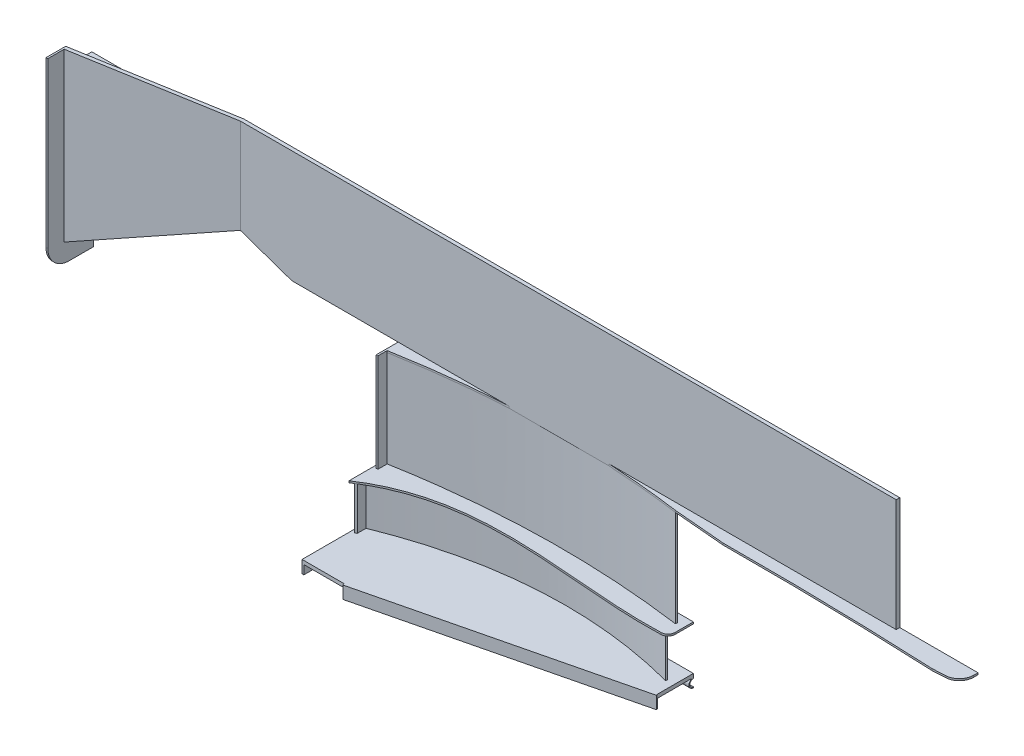
SolidWorks part; units mm, degrees
material "Elastyczna pianka poliuretanowa"
ref_plane "Płaszczyzna XY" through (0, 0, 0) normal (0, 0, 1) x (1, 0, 0)
ref_plane "Płaszczyzna XZ" through (0, 0, 0) normal (0, 1, 0) x (1, 0, 0)
ref_plane "Płaszczyzna YZ" through (0, 0, 0) normal (1, 0, 0) x (0, 0, -1)
sketch "Szkic1" plane through (0, 0, 0) normal (0, 1, 0) x (1, 0, 0)
  line L0 (212.0804, -65) -> (-1629.5, -65)
  line L1 (212.0804, -65) -> (212.0804, -55)
  line L3 (212.0804, -55) -> (-1629.5, -55)
  line L4 (-1629.5, -55) -> (-1629.5, -65)
  dimension "D1" = 10
extrude "Dodanie-wyciągnięcie1" add sketch "Szkic1" against normal blind 315
sketch "Szkic2" plane through (0, -315, 0) normal (0, -1, 0) x (1, 0, 0)
  line L0 (-1189.8241, 55) -> (82.699, 55)
  line L1 (-1189.8241, 55) -> (-1189.8241, 215)
  line L4 (212.0804, 55) -> (-1629.5, 55) construction
  line L5 (82.699, 125) -> (82.699, 55)
  spline S0 degree 2 poles (82.699, 125) (-575.049, 24.9797) (-1189.8241, 215) knots 0 0 0 1 1 1
  dimension "D1" = 160
  dimension "D2" = 70
extrude "Dodanie-wyciągnięcie2" add sketch "Szkic2" along normal blind 5
sketch "Szkic4" plane through (0, -320, 0) normal (0, -1, 0) x (1, 0, 0)
  line L2 (-1182.1774, 101.7712) -> (-1182.1774, 96.7712)
  line L3 (-385.9493, 84.8158) -> (-385.9493, 79.8158)
  spline S0 degree 2 poles (-385.9493, 84.8158) (-787.3305, 30.0926) (-1182.1774, 101.7712) knots 0 0 0 1 1 1
  spline S1 degree 2 poles (-385.9493, 79.8158) (-787.3305, 25.0926) (-1182.1774, 96.7712) knots 0 0 0 1 1 1
  dimension "D3" = 5
  dimension "D1" = 5
  dimension "D2" = 5
extrude "Dodanie-wyciągnięcie4" add sketch "Szkic4" along normal blind 270
sketch "Szkic5" plane through (0, -590, 0) normal (0, -1, 0) x (1, 0, 0)
  line L6 (-1189.8241, 195) -> (-1189.8241, 55)
  line L7 (-1189.8241, 55) -> (-365.6656, 55)
  line L8 (-365.6656, 55) -> (-365.6656, 125)
  spline S0 degree 3 poles (-1189.8241, 195) (-948.4635, 33.502) (-627.9265, 141.4858) (-365.6656, 125) knots 0 0 0 0 1 1 1 1
  dimension "D2" = 70
  dimension "D1" = 140
extrude "Dodanie-wyciągnięcie5" add sketch "Szkic5" along normal blind 5
sketch "Szkic6" plane through (0, -595, 0) normal (0, -1, 0) x (1, 0, 0)
  line L1 (-1180.7317, 163.4647) -> (-1180.7317, 158.4647)
  line L2 (-386.7114, 111.4299) -> (-386.7114, 106.4299)
  spline S0 degree 2 poles (-386.7114, 111.4299) (-791.4105, 5.1463) (-1180.7317, 163.4647) knots 0 0 0 1 1 1
  spline S1 degree 2 poles (-386.7114, 106.4299) (-791.4105, 0.1463) (-1180.7317, 158.4647) knots 0 0 0 1 1 1
  dimension "D1" = 5
  dimension "D2" = 5
  dimension "D3" = 5
extrude "Dodanie-wyciągnięcie6" add sketch "Szkic6" along normal blind 120
sketch "Szkic7" plane through (0, -715, 0) normal (0, -1, 0) x (1, 0, 0)
  line L0 (-1189.8241, 55) -> (-365.6656, 55)
  line L1 (-365.6656, 55) -> (-365.6656, 155)
  line L2 (-365.6656, 155) -> (-1189.8241, 355)
  line L3 (-1189.8241, 355) -> (-1189.8241, 55)
  dimension "D1" = 100
  dimension "D2" = 300
extrude "Dodanie-wyciągnięcie7" add sketch "Szkic7" along normal blind 10
sketch "Szkic9" plane through (-1189.8241, 0, 0) normal (-1, 0, 0) x (0, 0, 1)
  line L1 (55, -725) -> (55, -727.5)
  line L2 (55, -750) -> (55, -747.5)
  line L3 (55, -725) -> (60, -725)
  line L4 (355, -725) -> (55, -725) construction
  line L5 (60, -725) -> (60, -726.0436)
  arc A0 (55, -750) -> (60, -726.0436) centre (55, -737.5) ccw
  arc A1 (55, -747.5) -> (55, -727.5) centre (55, -737.5) ccw
  dimension "D2" = 20
  dimension "D1" = 25
  dimension "D3" = 5
extrude "Dodanie-wyciągnięcie8" add sketch "Szkic9" against normal up to surface (824.1585 mm away) up to face at (-365.6656, -720, 105)
sketch "Szkic10" plane through (-1189.8241, 0, 0) normal (-1, 0, 0) x (0, 0, 1)
  line L1 (355, -715) -> (55, -715)
  line L2 (355, -715) -> (355, -750)
  line L3 (355, -750) -> (55, -750)
  line L4 (55, -715) -> (55, -750)
sketch "Szkic14" plane through (0, -315, 0) normal (0, -1, 0) x (-1, 0, 0)
  line L0 (-212.0804, -60) -> (-152.676, -65)
  line L1 (-212.0804, -65) -> (-212.0804, -55) construction
  line L2 (-82.699, -65) -> (-212.0804, -65) construction
  line L3 (-152.676, -65) -> (-157.0687, -100.1209)
  line L4 (-157.0687, -100.1209) -> (-228.0372, -94.1476)
  line L5 (-228.0372, -94.1476) -> (-212.0804, -60)
extrude "Wytnij-wyciągnięcie3" cut sketch "Szkic14" against normal blind 800
sketch "Szkic15" plane through (0, -315, 0) normal (0, -1, 0) x (1, 0, 0)
  line L0 (-1629.5, 60) -> (-1533.9911, 65)
  line L1 (-1629.5, 65) -> (-1189.8241, 65) construction
  line L2 (-1533.9911, 65) -> (-1548.7216, 115.3773)
  line L3 (-1548.7216, 115.3773) -> (-1654.5546, 99.5137)
  line L4 (-1654.5546, 99.5137) -> (-1629.5, 60)
extrude "Wytnij-wyciągnięcie4" cut sketch "Szkic15" against normal blind 800
sketch "Szkic17" plane through (0, 0, 0) normal (0, 0, 1) x (1, 0, 0)
  line L0 (212.0804, -300) -> (152.676, -315)
  line L1 (152.676, -315) -> (126.1433, -456.8936)
  line L2 (126.1433, -456.8936) -> (421.9863, -502.2244)
  line L3 (421.9863, -502.2244) -> (212.0804, -300)
extrude "Wytnij-wyciągnięcie6" cut sketch "Szkic17" along normal blind 800
sketch "Szkic18" plane through (0, 0, 0) normal (0, 0, 1) x (1, 0, 0)
  line L0 (-1629.5, -300) -> (-1533.9911, -315)
  line L1 (-1533.9911, -315) -> (-1533.9911, -431.4085)
  line L2 (-1533.9911, -431.4085) -> (-1704.1876, -396.776)
  line L3 (-1704.1876, -396.776) -> (-1629.5, -300)
extrude "Wytnij-wyciągnięcie7" cut sketch "Szkic18" along normal blind 800
ref_plane "Płaszczyzna1" through (0, 0, 60) normal (0, 0, -1) x (-1, 0, 0)
ref_plane "Płaszczyzna2" through (0, 0, 70) normal (0, 0, -1) x (-1, 0, 0)
sketch "Szkic21" plane through (0, 0, 60) normal (0, 0, -1) x (-1, 0, 0)
  line L0 (1182.1774, -590) -> (1182.1774, -320) construction
  line L1 (1182.1774, -452.5) -> (385.9493, -452.5)
  line L2 (1182.1774, -452.5) -> (1182.1774, -457.5)
  line L3 (1182.1774, -457.5) -> (385.9493, -457.5)
  line L4 (385.9493, -452.5) -> (385.9493, -457.5)
  line L5 (385.9493, -590) -> (385.9493, -320) construction
  line L6 (1182.1774, -590) -> (385.9493, -590) construction
  line L7 (1182.1774, -521.25) -> (385.9493, -521.25)
  line L8 (1182.1774, -521.25) -> (1182.1774, -526.25)
  line L9 (1182.1774, -526.25) -> (385.9493, -526.25)
  line L10 (385.9493, -521.25) -> (385.9493, -526.25)
  line L11 (1182.1774, -383.75) -> (385.9493, -383.75)
  line L12 (1182.1774, -383.75) -> (1182.1774, -388.75)
  line L13 (1182.1774, -388.75) -> (385.9493, -388.75)
  line L14 (385.9493, -383.75) -> (385.9493, -388.75)
  line L15 (1189.8241, -590) -> (365.6656, -590) construction
  dimension "D1" = 5
  dimension "D2" = 5
  dimension "D3" = 5
  dimension "D4" = 63.75
  dimension "D5" = 132.5
  dimension "D6" = 201.25
sketch "Szkic22" plane through (0, 0, 70) normal (0, 0, -1) x (-1, 0, 0)
  line L0 (386.7114, -715) -> (386.7114, -595) construction
  line L1 (386.7114, -631) -> (1180.7317, -631)
  line L2 (386.7114, -631) -> (386.7114, -636)
  line L3 (386.7114, -636) -> (1180.7317, -636)
  line L4 (1180.7317, -631) -> (1180.7317, -636)
  line L5 (1180.7317, -715) -> (1180.7317, -595) construction
  line L6 (1189.8241, -715) -> (365.6656, -715) construction
  line L7 (1180.7317, -673) -> (386.7114, -673)
  line L8 (1180.7317, -673) -> (1180.7317, -678)
  line L9 (1180.7317, -678) -> (386.7114, -678)
  line L10 (386.7114, -673) -> (386.7114, -678)
  dimension "D1" = 5
  dimension "D2" = 5
  dimension "D3" = 37
  dimension "D4" = 79
sketch "Szkic24" plane through (0, 0, 0) normal (0, 1, 0) x (1, 0, 0)
  line L0 (212.0804, -60) -> (152.676, -65) construction
  line L1 (212.0804, -60) -> (152.676, -65)
  line L2 (152.676, -65) -> (212.0804, -65)
  line L3 (212.0804, -65) -> (212.0804, -60)
extrude "Dodanie-wyciągnięcie15" add sketch "Szkic24" against normal up to surface (315 mm away)
sketch "Szkic25" plane through (0, -725, 0) normal (0, -1, 0) x (1, 0, 0)
  line L0 (-1071.8568, 326.3727) -> (-1189.8241, 326.3727)
  line L1 (-365.6656, 155) -> (-1189.8241, 355) construction
  line L2 (-1189.8241, 355) -> (-1189.8241, 60) construction
  line L3 (-1189.8241, 326.3727) -> (-1281.2859, 396.2551)
  line L4 (-1281.2859, 396.2551) -> (-1102.8266, 410.2769)
  line L5 (-1102.8266, 410.2769) -> (-1071.8568, 326.3727)
extrude "Wytnij-wyciągnięcie8" cut sketch "Szkic25" against normal mid plane 80
sketch "Szkic26" plane through (15.1859, 0, 62.5781) normal (0.2358, 0, 0.9718) x (0.9718, 0, -0.2358)
  line L0 (-391.9052, -715) -> (-1118.5926, -715) construction
  line L1 (-391.9052, -715) -> (-1118.5926, -715)
  line L2 (-1118.5926, -715) -> (-1118.5926, -750)
  line L3 (-1118.5926, -750) -> (-391.9052, -750)
  line L4 (-391.9052, -750) -> (-391.9052, -715)
  dimension "D1" = 35
extrude "Dodanie-wyciągnięcie16" add sketch "Szkic26" along normal blind 5
extrude "Dodanie-wyciągnięcie17" [suppressed] add sketch "Szkic21" against normal up to surface
extrude "Dodanie-wyciągnięcie18" [suppressed] add sketch "Szkic22" against normal up to surface
extrude "Dodanie-wyciągnięcie19" add sketch "Szkic10" against normal blind 5
sketch "Szkic27" plane through (-1184.8241, 0, 0) normal (1, 0, 0) x (0, 0, -1)
  line L0 (-55, -747.5) -> (-38.9515, -762.249)
  line L1 (-38.9515, -762.249) -> (-37.3436, -710.6562)
  line L2 (-37.3436, -710.6562) -> (-55, -727.5)
  arc A0 (-55, -727.5) -> (-55, -747.5) centre (-55, -737.5) ccw construction
  arc A1 (-55, -727.5) -> (-55, -747.5) centre (-55, -737.5) ccw
extrude "Wytnij-wyciągnięcie10" cut sketch "Szkic27" against normal blind 10
sketch "Szkic28" plane through (0, -725, 0) normal (0, -1, 0) x (1, 0, 0)
  line L0 (-1184.8241, 326.3727) -> (-1217.6501, 326.3727)
  line L1 (-1217.6501, 326.3727) -> (-1219.4064, 378.7375)
  line L2 (-1219.4064, 378.7375) -> (-1162.0341, 378.7375)
  line L3 (-1162.0341, 378.7375) -> (-1184.8241, 326.3727)
extrude "Wytnij-wyciągnięcie11" cut sketch "Szkic28" against normal mid plane 70
sketch "Szkic29" plane through (0, -320, 0) normal (0, -1, 0) x (1, 0, 0)
  line L0 (-385.9493, 84.8158) -> (-385.9493, 334.4072)
  line L1 (-385.9493, 334.4072) -> (-1182.1774, 473.4681)
  line L2 (-1182.1774, 473.4681) -> (-1313.5858, 196.6459)
  line L3 (-1313.5858, 196.6459) -> (-1213.5139, 101.7712)
  line L4 (-1213.5139, 101.7712) -> (-1182.1774, 101.7712)
  line L5 (-592.49, 65) -> (-871.6388, 65)
  parabola Q0 (-385.9493, 84.8158) -> (-1182.1774, 101.7712) focus (-797.0532, 1314.433) apex (-861.6689, 64.4647) construction
  parabola Q1 (-385.9493, 84.8158) -> (-592.49, 65) focus (-797.0532, 1314.433) apex (-861.6689, 64.4647)
  parabola Q2 (-871.6388, 65) -> (-1182.1774, 101.7712) focus (-797.0532, 1314.433) apex (-861.6689, 64.4647)
extrude "Wytnij-wyciągnięcie13" cut sketch "Szkic29" against normal blind 70
sketch "Szkic30" plane through (0, 0, 101.7712) normal (0, 0, 1) x (1, 0, 0)
  line L0 (-1182.1774, -315) -> (-1182.1774, -336.9942)
  line L1 (-1182.1774, -590) -> (-1182.1774, -320) construction
  line L2 (-1182.1774, -336.9942) -> (-1198.8749, -336.9942)
  line L3 (-1198.8749, -336.9942) -> (-1198.8749, -315)
  line L4 (-1533.9911, -315) -> (-1189.8241, -315) construction
  line L5 (-1198.8749, -315) -> (-1182.1774, -315)
extrude "Wytnij-wyciągnięcie14" cut sketch "Szkic30" against normal blind 70
sketch "Szkic31" plane through (0, -320, 0) normal (0, -1, 0) x (1, 0, 0)
  line L0 (82.699, 125) -> (-385.9493, 90.5791)
  line L1 (-385.9493, 90.5791) -> (-211.5905, 70.3012)
  line L2 (-211.5905, 70.3012) -> (82.699, 100.9519)
  line L3 (82.699, 55) -> (82.699, 125) construction
  line L4 (82.699, 100.9519) -> (82.699, 125)
extrude "Dodanie-wyciągnięcie20" add sketch "Szkic31" against normal blind 5
sketch "Szkic32" plane through (0, -315, 0) normal (0, 1, 0) x (1, 0, 0)
  line L0 (-385.9493, -84.8158) -> (82.699, -125)
  line L1 (82.699, -125) -> (43.2512, -321.646)
  line L2 (43.2512, -321.646) -> (-385.9493, -284.8442)
  line L3 (-385.9493, -284.8442) -> (-385.9493, -84.8158)
extrude "Wytnij-wyciągnięcie15" cut sketch "Szkic32" against normal blind 5
fillet "Zaokrąglenie1" [suppressed] radius 20
fillet "Zaokrąglenie2" radius 20 1 edges at (-365.6656, -592.5, 125)
sketch "Szkic33" plane through (-1182.1774, 0, 0) normal (-1, 0, 0) x (0, 0, 1)
  line L0 (65, -315) -> (101.7712, -315) construction
  line L1 (96.7712, -315) -> (126.7712, -315)
  line L2 (96.7712, -315) -> (96.7712, -590)
  line L3 (96.7712, -590) -> (126.7712, -590)
  line L4 (126.7712, -315) -> (126.7712, -590)
  dimension "D1" = 30
extrude "Dodanie-wyciągnięcie21" add sketch "Szkic33" against normal blind 5
sketch "Szkic34" plane through (-1180.7317, 0, 0) normal (-1, 0, 0) x (0, 0, 1)
  line L2 (158.4647, -595) -> (158.4647, -715)
  line L5 (158.4647, -595) -> (195, -595)
  line L6 (195, -595) -> (195, -715)
  line L7 (326.3727, -715) -> (55, -715) construction
  line L8 (195, -715) -> (158.4647, -715)
extrude "Dodanie-wyciągnięcie22" add sketch "Szkic34" against normal blind 5
sketch "Szkic35" plane through (0, 0, 0) normal (0, 1, 0) x (1, 0, 0)
  line L0 (-1533.9911, -65) -> (-1533.9911, -13.0362)
  line L1 (-1533.9911, -13.0362) -> (-1638.7677, -13.0362)
  line L2 (-1638.7677, -13.0362) -> (-1638.7677, -80.7734)
  line L3 (-1638.7677, -80.7734) -> (-1533.9911, -80.7734)
  line L4 (-1533.9911, -80.7734) -> (-1533.9911, -65)
extrude "Wytnij-wyciągnięcie16" cut sketch "Szkic35" against normal through all
sketch "Szkic36" plane through (-1533.9911, 0, 0) normal (-1, 0, 0) x (0, 0, 1)
  line L4 (55, 0) -> (55, -315)
  line L5 (55, -315) -> (65, -315)
  line L6 (65, -315) -> (65, 0)
  line L7 (65, 0) -> (55, 0)
  line L8 (55, 0) -> (55, -315)
  line L9 (55, -315) -> (65, -315)
  line L10 (65, -315) -> (65, 0)
  line L11 (65, 0) -> (55, 0)
  dimension "D1" = 0
extrude "Dodanie-wyciągnięcie23" add sketch "Szkic36" along normal blind 90
sketch "Szkic37" plane through (0, 0, 65) normal (0, 0, 1) x (1, 0, 0)
  line L0 (-1623.9911, -265) -> (-1480, -315)
  line L1 (-1623.9911, -315) -> (-1623.9911, 0) construction
  line L2 (-1623.9911, -265) -> (-1686.659, -216.1907)
  line L3 (-1686.659, -216.1907) -> (-1743.661, -471.7498)
  line L4 (-1743.661, -471.7498) -> (-1582.1553, -427.0982)
  line L5 (-1582.1553, -427.0982) -> (-1480, -315)
  dimension "D1" = 50
extrude "Wytnij-wyciągnięcie17" cut sketch "Szkic37" against normal blind 15
sketch "Szkic38" plane through (0, 0, 0) normal (0, 1, 0) x (1, 0, 0)
  line L0 (-1623.9911, -65) -> (-1623.9911, -55)
  line L2 (-1623.9911, -65) -> (-2049.8495, -138.2373)
  line L3 (-1623.9911, -55) -> (-2049.8495, -128.2373)
  line L4 (-2049.8495, -128.2373) -> (-2049.8495, -138.2373)
extrude "Dodanie-wyciągnięcie24" add sketch "Szkic38" against normal blind 470
sketch "Szkic39" plane through (0, 0, 65) normal (0, 0, 1) x (1, 0, 0)
  line L0 (-1623.9911, -265) -> (-2049.8495, -470)
  line L1 (-2049.8495, -470) -> (-2049.8495, -632.3644)
  line L2 (-2049.8495, -632.3644) -> (-1604.6157, -507.9476)
  line L3 (-1604.6157, -507.9476) -> (-1623.9911, -265)
extrude "Wytnij-wyciągnięcie18" cut sketch "Szkic39" along normal mid plane 470
sketch "Szkic40" plane through (0, 0, 55) normal (0, 0, -1) x (-1, 0, 0)
  line L0 (1623.9911, -265) -> (2049.8495, -470)
  line L1 (2049.8495, -470) -> (2049.8495, -465)
  line L2 (2049.8495, -470) -> (2049.8495, 0) construction
  line L3 (2049.8495, -465) -> (1623.9911, -260)
  line L4 (1623.9911, 0) -> (1623.9911, -265) construction
  line L5 (1623.9911, -260) -> (1623.9911, -265)
  dimension "D1" = 5
extrude "Dodanie-wyciągnięcie25" add sketch "Szkic40" against normal up to surface (73.2373 mm away)
sketch "Szkic41" plane through (0, -315, 0) normal (0, -1, 0) x (1, 0, 0)
  line L1 (-2049.8495, 55) -> (-2049.8495, 138.2373) construction
  line L2 (-2049.8495, 88.2373) -> (-1623.9911, 55)
  line L3 (-2049.8495, 88.2373) -> (-2144.2103, 76.6484)
  line L4 (-2144.2103, 76.6484) -> (-2116.8993, -145.7257)
  line L5 (-2116.8993, -145.7257) -> (-1610.4163, -96.1255)
  line L6 (-1610.4163, -96.1255) -> (-1623.9911, 55)
extrude "Wytnij-wyciągnięcie19" [suppressed] cut sketch "Szkic41" against normal mid plane 470
sketch "Szkic42" plane through (0, 0, 55) normal (0, 0, -1) x (-1, 0, 0)
  line L0 (1623.9911, 0) -> (1623.9911, -260) construction
  line L1 (2049.8495, -465) -> (2049.8495, 0) construction
  line L2 (1623.9911, -244.3551) -> (1623.9911, -239.3551)
  line L3 (2049.8495, -406.3404) -> (2049.8495, -401.3404)
  line L4 (1623.9911, -200) -> (1623.9911, -205)
  line L5 (2049.8495, -294.9832) -> (2049.8495, -299.9832)
  line L6 (1623.9911, -50) -> (2049.8495, -50)
  line L7 (1623.9911, 0) -> (2049.8495, 0) construction
  line L8 (1623.9911, -50) -> (1623.9911, -55)
  line L9 (1623.9911, -150) -> (2049.8495, -150)
  line L10 (1623.9911, -55) -> (2049.8495, -55)
  line L11 (2049.8495, -55) -> (2049.8495, -50)
  line L12 (2049.8495, -150) -> (2049.8495, -145)
  line L13 (2049.8495, -145) -> (1623.9911, -145)
  line L14 (1623.9911, -145) -> (1623.9911, -150)
  spline S0 degree 2 poles (1623.9911, -244.3551) (1855.4275, -278.9095) (2049.8495, -406.3404) knots 0 0 0 1 1 1
  spline S1 degree 2 poles (2049.8495, -401.3404) (1855.4275, -273.9095) (1623.9911, -239.3551) knots 0 0 0 1 1 1
  spline S2 degree 2 poles (1623.9911, -205) (1843.1035, -226.1009) (2049.8495, -299.9832) knots 0 0 0 1 1 1
  spline S3 degree 2 poles (1623.9911, -200) (1843.1035, -221.1009) (2049.8495, -294.9832) knots 0 0 0 1 1 1
  dimension "D1" = 5
  dimension "D2" = 5
  dimension "D3" = 5
  dimension "D4" = 5
  dimension "D5" = 5
  dimension "D6" = 5
  dimension "D7" = 50
  dimension "D8" = 5
  dimension "D9" = 150
  dimension "D10" = 50
  dimension "D11" = 5
extrude "Dodanie-wyciągnięcie26" add sketch "Szkic42" against normal up to surface up to face at (-1836.9203, -181.25, 91.6187)
sketch "Szkic43" [suppressed] plane through (-2049.8495, 0, 0) normal (-1, 0, 0) x (0, 0, 1)
  line L0 (128.2373, 0) -> (178.2373, 0)
  line L1 (375.099, 0) -> (140.9039, 0) construction
  line L3 (178.2373, 0) -> (178.2373, -465)
  line L4 (88.2373, -515) -> (128.2373, -515)
  line L5 (128.2373, 0) -> (128.2373, -465)
  line L8 (88.2373, -465) -> (88.2373, -515)
  line L9 (128.2373, -465) -> (88.2373, -465)
  arc A0 (128.2373, -515) -> (178.2373, -465) centre (128.2373, -465) ccw
  line M9 (88.2373, -465) -> (88.2373, -470)
  line M10 (88.2373, -470) -> (138.2373, -470)
  line M11 (138.2373, -470) -> (138.2373, 0)
  line M12 (138.2373, 0) -> (128.2373, 0)
  line M13 (128.2373, 0) -> (128.2373, -50)
  line M17 (128.2373, -55) -> (128.2373, -145)
  line M21 (128.2373, -150) -> (128.2373, -294.9832)
  line M25 (128.2373, -299.9832) -> (128.2373, -401.3404)
  line M29 (128.2373, -406.3404) -> (128.2373, -465)
  line M30 (128.2373, -465) -> (88.2373, -465)
  dimension "D3" = 50
  dimension "D1" = 50
  dimension "D2" = 50
extrude "Dodanie-wyciągnięcie27" [suppressed] add sketch "Szkic43" against normal blind 5 contours L4 A0 L3 L0 L8 M11 M10 | L5 M13 M17 M21 M25 M29 M30 M9 M10 M11 M12
sketch "Szkic44" plane through (0, 0, 55) normal (0, 0, -1) x (-1, 0, 0)
  line L0 (2049.8495, -406.3404) -> (2049.8495, -401.3404) construction
  line L1 (2049.8495, -406.3404) -> (2049.8495, -401.3404)
  line L2 (1623.9911, -239.3551) -> (1623.9911, -244.3551)
  parabola Q0 (2049.8495, -406.3404) -> (1623.9911, -244.3551) focus (1669.2994, -790.1518) apex (1861.4257, -308.0681) construction
  parabola Q1 (1623.9911, -239.3551) -> (2049.8495, -401.3404) focus (1669.2994, -785.1518) apex (1861.4257, -303.0681) construction
  parabola Q2 (2049.8495, -406.3404) -> (1623.9911, -244.3551) focus (1669.2994, -790.1518) apex (1861.4257, -308.0681)
  parabola Q3 (1623.9911, -239.3551) -> (2049.8495, -401.3404) focus (1669.2994, -785.1518) apex (1861.4257, -303.0681)
extrude "Wytnij-wyciągnięcie20" cut sketch "Szkic44" against normal up to surface (73.2373 mm away)
sketch "Szkic45" plane through (-2049.8495, 0, 0) normal (-1, 0, 0) x (0, 0, 1)
  line L0 (128.2373, 0) -> (183.2373, 0)
  line L1 (55, -465) -> (55, -520)
  line L2 (183.2373, 0) -> (183.2373, -460)
  line L3 (123.2373, -520) -> (55, -520)
  line L4 (128.2373, 0) -> (128.2373, -465)
  line L5 (128.2373, -465) -> (55, -465)
  arc A0 (183.2373, -460) -> (123.2373, -520) centre (123.2373, -460) cw
  dimension "D3" = 60
  dimension "D1" = 55
  dimension "D2" = 55
extrude "Dodanie-wyciągnięcie28" add sketch "Szkic45" against normal blind 5
sketch "Szkic47" plane through (0, -315, 0) normal (0, -1, 0) x (1, 0, 0)
  line L1 (152.676, 65) -> (212.0804, 65)
  line L2 (152.676, 65) -> (152.676, 55)
  line L3 (152.676, 55) -> (212.0804, 55)
  line L4 (212.0804, 65) -> (212.0804, 55)
extrude "Dodanie-wyciągnięcie29" add sketch "Szkic47" against normal blind 20
sketch "Szkic48" plane through (0, -315, 0) normal (0, -1, 0) x (1, 0, 0)
  line L1 (82.699, 125) -> (431.0804, 105)
  line L2 (82.699, 125) -> (82.699, 55)
  line L3 (82.699, 55) -> (212.0804, 55)
  line L4 (212.0804, 55) -> (431.0804, 55)
  line L5 (431.0804, 55) -> (431.0804, 105)
  dimension "D2" = 219
extrude "Dodanie-wyciągnięcie30" add sketch "Szkic48" along normal blind 5
sketch "Szkic49" plane through (0, -320, 0) normal (0, -1, 0) x (1, 0, 0)
  line L4 (82.699, 125) -> (-385.9493, 84.8158) construction
  line L5 (431.0804, 105) -> (82.699, 125) construction
  line L6 (-29.8058, 115.3533) -> (-93.4416, 240.9759)
  line L7 (-93.4416, 240.9759) -> (363.6464, 245.2535)
  line L8 (363.6464, 245.2535) -> (300.769, 112.481)
  spline S0 degree 2 poles (-29.8058, 115.3533) (135.498, 122.2199) (300.769, 112.481) knots 0 0 0 1 1 1
extrude "Wytnij-wyciągnięcie21" cut sketch "Szkic49" against normal blind 5
fillet "Zaokrąglenie3" radius 40 1 edges at (431.0804, -317.5, 105)
sketch "Szkic50" plane through (0, -320, 0) normal (0, -1, 0) x (1, 0, 0)
  line L0 (-29.8058, 115.3533) -> (-385.9493, 84.8158) construction
  line L1 (393.373, 107.1647) -> (290.779, 113.0545) construction
  line L2 (-240.1724, 97.3154) -> (-253.2335, 230.8199)
  line L3 (-253.2335, 230.8199) -> (380.2655, 230.8199)
  line L4 (380.2655, 230.8199) -> (357.2059, 109.241)
  spline S0 degree 2 poles (-240.1724, 97.3154) (58.728, 95.461) (357.2059, 109.241) knots 0 0 0 1 1 1
extrude "Wytnij-wyciągnięcie22" cut sketch "Szkic50" against normal blind 10
sketch "Szkic53" plane through (0, -595, 0) normal (0, 1, 0) x (1, 0, 0)
  line L3 (-1180.7317, -189.0665) -> (-1180.7317, -195)
  line L4 (-1180.7317, -195) -> (-1175.7317, -195)
  line L5 (-1175.7317, -195) -> (-1175.7317, -185.9289)
  line L6 (-1180.7317, -189.0665) -> (-1180.7317, -195)
  line L7 (-1180.7317, -195) -> (-1175.7317, -195)
  line L8 (-1175.7317, -195) -> (-1175.7317, -185.9289)
  arc A1 (-1175.7317, -185.9289) -> (-1180.7317, -189.0665) centre (-927.8222, -586.548) ccw
  arc A2 (-1175.7317, -185.9289) -> (-1180.7317, -189.0665) centre (-927.8222, -586.548) ccw
  dimension "D1" = 0
extrude "Wytnij-wyciągnięcie23" cut sketch "Szkic53" against normal up to surface (120 mm away) up to face at (-802.5715, -715, 201.2623)
